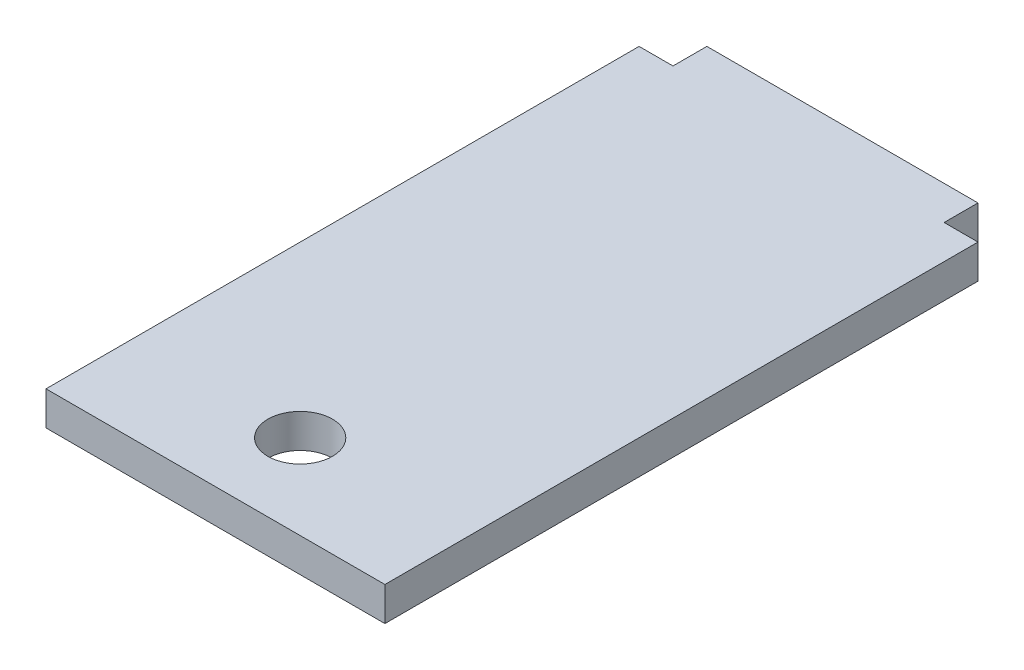
SolidWorks part; units mm, degrees
ref_plane "Front Plane" through (0, 0, 0) normal (0, 0, 1) x (1, 0, 0)
ref_plane "Top Plane" through (0, 0, 0) normal (0, 1, 0) x (1, 0, 0)
ref_plane "Right Plane" through (0, 0, 0) normal (1, 0, 0) x (0, 0, -1)
sketch "Sketch1" plane through (0, 0, 0) normal (0, 1, 0) x (1, 0, 0)
  line L0 (0, 87.5) -> (5, 87.5)
  line L1 (0, 0) -> (50, 0)
  line L2 (0, 0) -> (0, 87.5)
  line L3 (5, 92.5) -> (45, 92.5)
  line L4 (50, 0) -> (50, 87.5)
  line L5 (5, 92.5) -> (5, 87.5)
  line L6 (50, 87.5) -> (45, 87.5)
  line L7 (45, 87.5) -> (45, 92.5)
  line L8 (0, 12.5) -> (50, 12.5) construction
  circle A0 centre (25, 12.5) radius 4.7625
  dimension "D6" = 9.525
  dimension "D1" = 87.5
  dimension "D2" = 5
  dimension "D3" = 5
  dimension "D4" = 5
  dimension "D5" = 50
  dimension "D7" = 80
extrude "Hammer" add sketch "Sketch1" along normal blind 5
